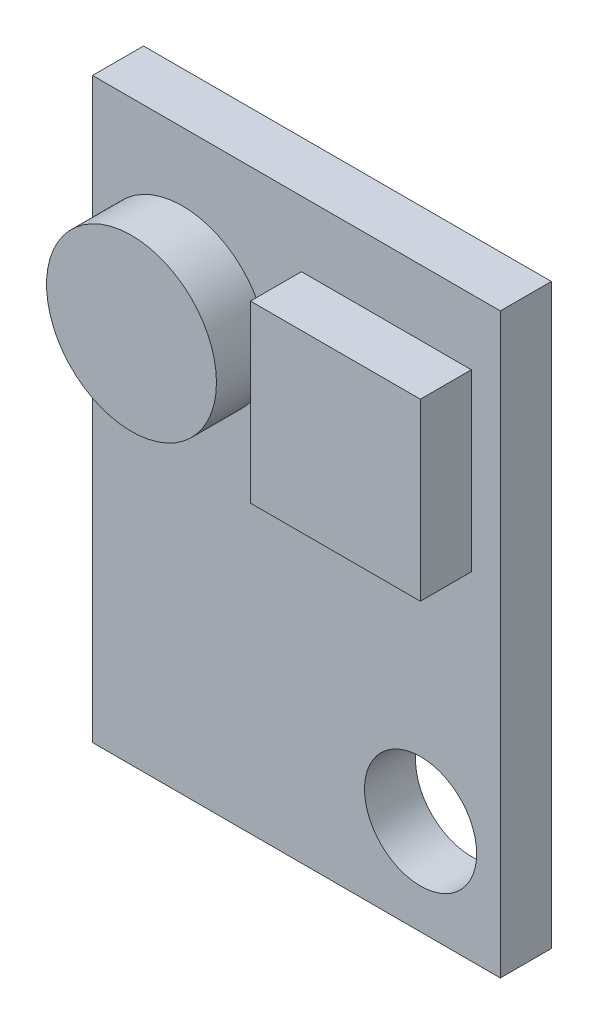
SolidWorks part; units mm, degrees
ref_plane "Plano frontal" through (0, 0, 0) normal (0, 0, 1) x (1, 0, 0)
ref_plane "Plano superior" through (0, 0, 0) normal (0, 1, 0) x (1, 0, 0)
ref_plane "Plano direito" through (0, 0, 0) normal (1, 0, 0) x (0, 0, -1)
sketch "Esboço1" plane through (0, 0, 0) normal (0, 0, 1) x (1, 0, 0)
  line L1 (-6, 8.5) -> (6, 8.5)
  line L2 (-6, 8.5) -> (-6, -8.5)
  line L3 (-6, -8.5) -> (6, -8.5)
  line L4 (6, 8.5) -> (6, -8.5)
  line L5 (-6, 8.5) -> (6, -8.5) construction
  line L6 (-6, -8.5) -> (6, 8.5) construction
  circle A0 centre (3.6528, -5.6823) radius 1.65
  point P0 (0, 0)
  point P8 (3.6528, -5.6823)
  dimension "D3" = 3.3
  dimension "D1" = 17
  dimension "D2" = 12
extrude "Ressalto-extrusão1" add sketch "Esboço1" along normal blind 1.5
sketch "Esboço2" plane through (0, 0, 1.5) normal (0, 0, 1) x (1, 0, 0)
  line L1 (0.1463, 6.5728) -> (5.1463, 6.5728)
  line L2 (0.1463, 6.5728) -> (0.1463, 1.4248)
  line L3 (0.1463, 1.4248) -> (5.1463, 1.4248)
  line L4 (5.1463, 6.5728) -> (5.1463, 1.4248)
  line L5 (0.1463, 6.5728) -> (5.1463, 1.4248) construction
  line L6 (0.1463, 1.4248) -> (5.1463, 6.5728) construction
  circle A0 centre (-3.3537, 3.9988) radius 2.5
  point P2 (2.6463, 3.9988)
  dimension "D2" = 5
  dimension "D1" = 5
  dimension "D3" = 6
extrude "Ressalto-extrusão2" add sketch "Esboço2" along normal blind 1.5
